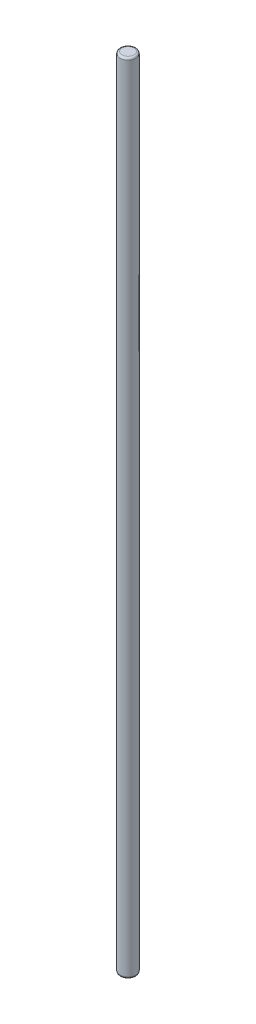
SolidWorks part; units mm, degrees
material "Chrome Stainless Steel"
ref_plane "Front Plane" through (0, 0, 0) normal (0, 0, 1) x (1, 0, 0)
ref_plane "Top Plane" through (0, 0, 0) normal (0, 1, 0) x (1, 0, 0)
ref_plane "Right Plane" through (0, 0, 0) normal (1, 0, 0) x (0, 0, -1)
sketch "Sketch1" plane through (0, 0, 0) normal (0, 1, 0) x (1, 0, 0)
  circle A0 centre (0, 0) radius 4
extrude "Boss-Extrude1" add sketch "Sketch1" along normal blind 400
fillet "Fillet2" radius 1 2 edges at (0, 0, 4) (0, 400, 4)
